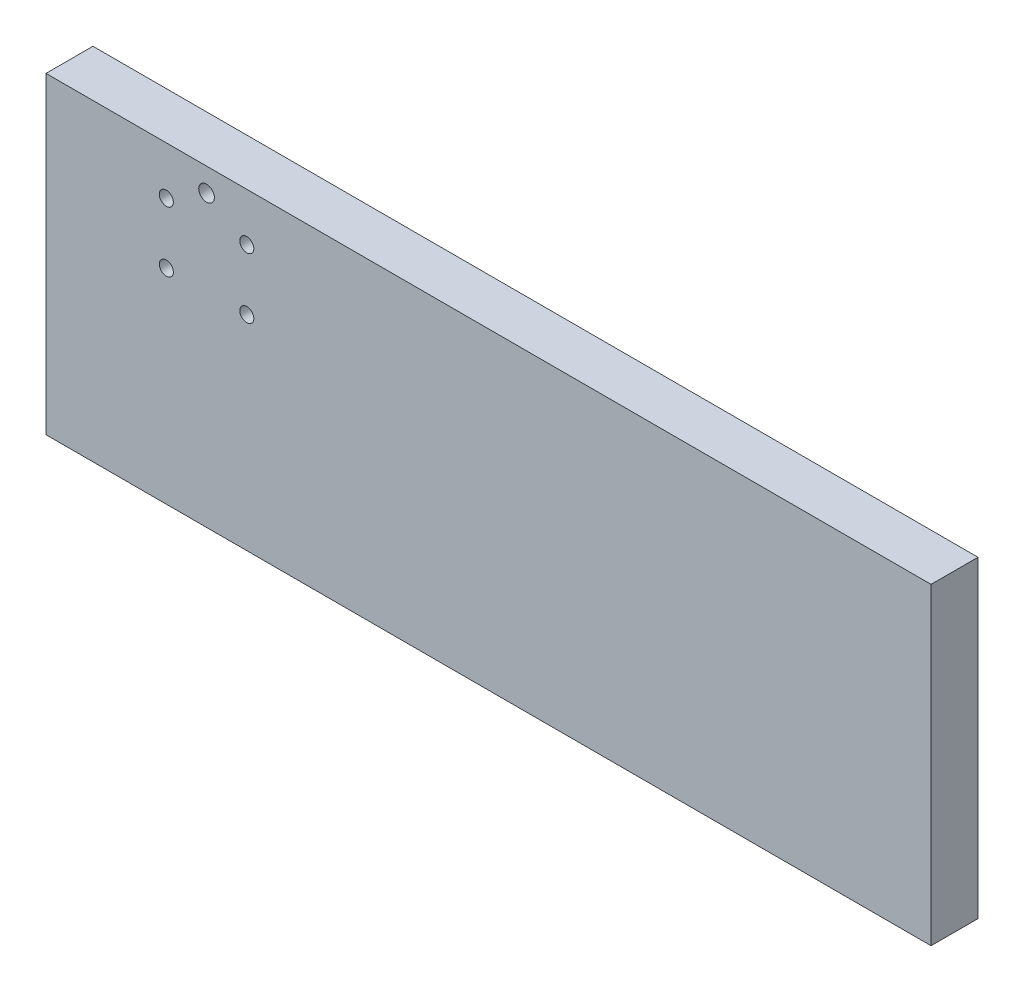
SolidWorks part; units mm, degrees
ref_plane "Front Plane" through (0, 0, 0) normal (0, 0, 1) x (1, 0, 0)
ref_plane "Top Plane" through (0, 0, 0) normal (0, 1, 0) x (1, 0, 0)
ref_plane "Right Plane" through (0, 0, 0) normal (1, 0, 0) x (0, 0, -1)
sketch "Sketch1" plane through (0, 0, 0) normal (0, 0, 1) x (1, 0, 0)
  line L1 (0, 0) -> (359.156, 0)
  line L2 (0, 0) -> (0, 127)
  line L3 (0, 127) -> (359.156, 127)
  line L4 (359.156, 0) -> (359.156, 127)
  dimension "D1" = 127
  dimension "D2" = 359.156
extrude "Boss-Extrude1" add sketch "Sketch1" along normal blind 19.05
sketch "Sketch2" plane through (0, 0, 19.05) normal (0, 0, 1) x (1, 0, 0)
  circle A0 centre (48.8251, 82.9627) radius 2.8511
  circle A1 centre (48.8251, 107.5372) radius 2.8511
  circle A2 centre (81.4768, 107.5372) radius 2.8512
  circle A3 centre (81.4768, 82.9627) radius 2.8512
extrude "Cut-Extrude1" cut sketch "Sketch2" against normal up to next
sketch "Sketch3" plane through (0, 0, 0) normal (0, 0, -1) x (-1, 0, 0)
  line L0 (-65.151, 114.3) -> (-65.151, 117.475) construction
  line L1 (-58.6607, 114.3) -> (-71.6413, 114.3) construction
  circle A1 centre (-65.151, 117.475) radius 3.175
  dimension "D1" = 3.175
  dimension "D2" = 6.35
extrude "Cut-Extrude2" cut sketch "Sketch3" along normal blind 6.35 from surface at -19.05 starting at face at (84.328, 82.9627, 19.05)
